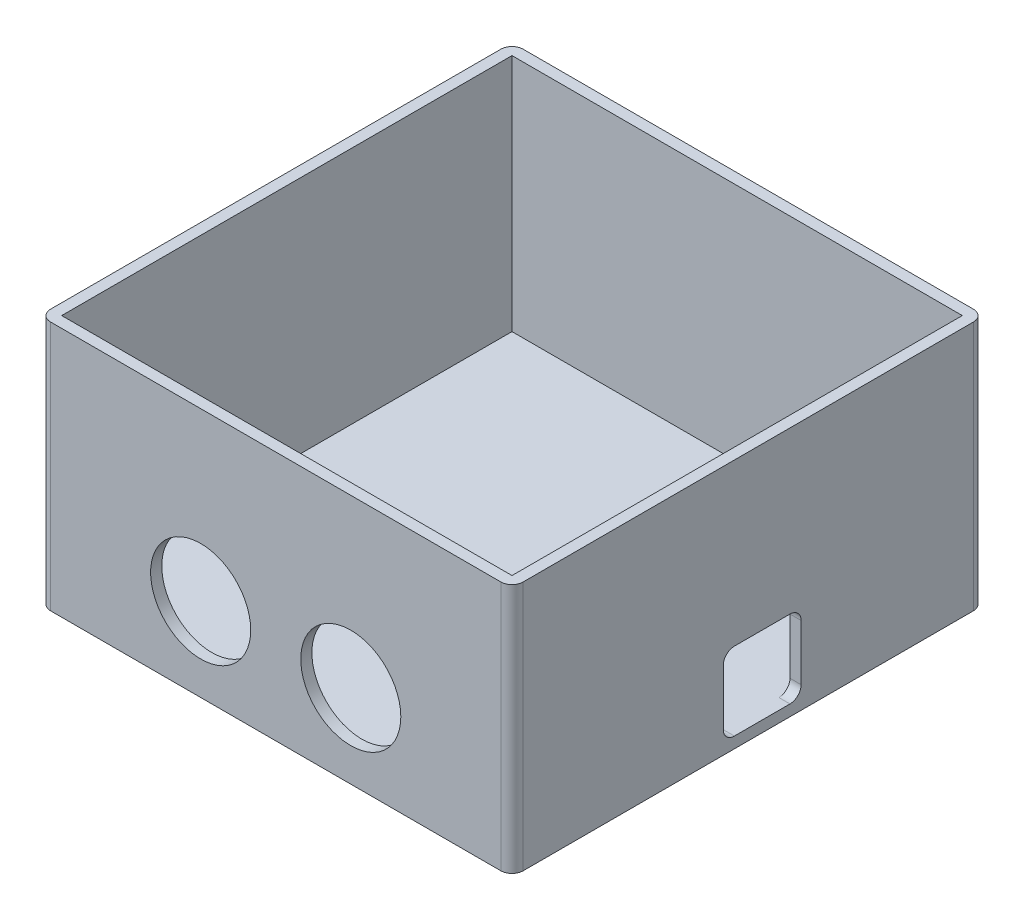
SolidWorks part; units mm, degrees
ref_plane "Front Plane" through (0, 0, 0) normal (0, 0, 1) x (1, 0, 0)
ref_plane "Top Plane" through (0, 0, 0) normal (0, 1, 0) x (1, 0, 0)
ref_plane "Right Plane" through (0, 0, 0) normal (1, 0, 0) x (0, 0, -1)
sketch "Sketch1" plane through (0, 0, 0) normal (0, 1, 0) x (1, 0, 0)
  line L1 (-36.9623, 23.5243) -> (48.0377, 23.5243)
  line L2 (-36.9623, 23.5243) -> (-36.9623, -61.4757)
  line L3 (-36.9623, -61.4757) -> (48.0377, -61.4757)
  line L4 (48.0377, 23.5243) -> (48.0377, -61.4757)
  dimension "D1" = 85
  dimension "D2" = 85
extrude "Boss-Extrude1" add sketch "Sketch1" along normal blind 2 contours L4 L3 L2 L1
sketch "Sketch2" plane through (0, 2, 0) normal (0, 1, 0) x (1, 0, 0)
  line L0 (-36.9623, 23.5243) -> (-36.9623, -61.4757) construction
  line L1 (-34.9623, 21.5243) -> (46.0377, 21.5243)
  line L2 (-34.9623, 21.5243) -> (-34.9623, -59.4757)
  line L3 (-34.9623, -59.4757) -> (46.0377, -59.4757)
  line L4 (46.0377, 21.5243) -> (46.0377, -59.4757)
  line L7 (-36.9623, 23.5243) -> (48.0377, 23.5243) construction
  line L8 (-36.9623, -61.4757) -> (48.0377, -61.4757) construction
  line L9 (-36.9623, 23.5243) -> (48.0377, 23.5243)
  line L10 (-36.9623, 23.5243) -> (-36.9623, -61.4757)
  line L11 (-36.9623, -61.4757) -> (48.0377, -61.4757)
  line L12 (48.0377, 23.5243) -> (48.0377, -61.4757)
  dimension "D1" = 2
  dimension "D4" = 2
  dimension "D2" = 2
  dimension "D3" = 2
extrude "Boss-Extrude2" add sketch "Sketch2" along normal blind 43
sketch "Sketch3" plane through (0, 0, 61.4757) normal (0, 0, 1) x (1, 0, 0)
  line L0 (-36.9623, 0) -> (48.0377, 0) construction
  line L1 (48.0377, 45) -> (48.0377, 0) construction
  circle A0 centre (-7.9623, 15) radius 9
  circle A1 centre (19.0377, 15) radius 9
  dimension "D2" = 18
  dimension "D3" = 18
  dimension "D1" = 27
  dimension "D4" = 15
  dimension "D5" = 29
extrude "Cut-Extrude1" cut sketch "Sketch3" against normal blind 2
sketch "Sketch4" plane through (48.0377, 0, 0) normal (1, 0, 0) x (0, 0, -1)
  line L0 (23.5243, 0) -> (-61.4757, 0) construction
  line L1 (-23.4757, 16) -> (-9.4757, 16)
  line L2 (-23.4757, 16) -> (-23.4757, 2)
  line L3 (-23.4757, 2) -> (-9.4757, 2)
  line L4 (-9.4757, 16) -> (-9.4757, 2)
  line L5 (23.5243, 45) -> (23.5243, 0) construction
  point P4 (-9.4757, 9)
  point P7 (-16.4757, 2)
  dimension "D1" = 14
  dimension "D2" = 14
  dimension "D3" = 9
  dimension "D4" = 40
extrude "Cut-Extrude2" cut sketch "Sketch4" against normal blind 2
fillet "Fillet1" radius 2 8 edges at (47.0377, 2, 9.4757) (47.0377, 16, 9.4757) (47.0377, 16, 23.4757) (47.0377, 2, 23.4757) (48.0377, 22.5, -23.5243) (-36.9623, 22.5, -23.5243) (-36.9623, 22.5, 61.4757) (48.0377, 22.5, 61.4757)
equation "\"Box width\" = 85"
equation "\"Box length\" = 85"
equation "\"Box height\"= 45"
equation "\"Sensor hole diameter\"= 18"
equation "\"Sensor Hole width\"= 27"
equation "\"Sensor height\"= 15"
equation "\"Power width\"= 14"
equation "\"D1@Sketch1\"=\"Box width\""
equation "\"D2@Sketch1\"=\"Box length\""
equation "\"Thick\"= 2"
equation "\"D1@Boss-Extrude1\"=\"Thick\""
equation "\"D1@Sketch2\"=\"Thick\""
equation "\"D4@Sketch2\"=\"Thick\""
equation "\"D1@Boss-Extrude2\"=\"Box height\"-\"Thick\""
equation "\"D1@Sketch3\"=\"Sensor Hole width\""
equation "\"D2@Sketch3\"=\"Sensor hole diameter\""
equation "\"D3@Sketch3\"=\"Sensor hole diameter\""
equation "\"D4@Sketch3\"=\"Sensor height\""
equation "\"D5@Sketch3\"=(\"Box width\"-\"Sensor Hole width\")/2"
equation "\"D1@Cut-Extrude1\"=\"Thick\""
equation "\"power height\"= 9"
equation "\"power from rear\"= 40"
equation "\"D2@Sketch4\"=\"Power width\""
equation "\"D3@Sketch4\"=\"power height\""
equation "\"D4@Sketch4\"=\"power from rear\""
equation "\"D1@Cut-Extrude2\"=\"Thick\""
equation "\"D2@Sketch2\"=\"Thick\""
equation "\"D3@Sketch2\"=\"Thick\""
